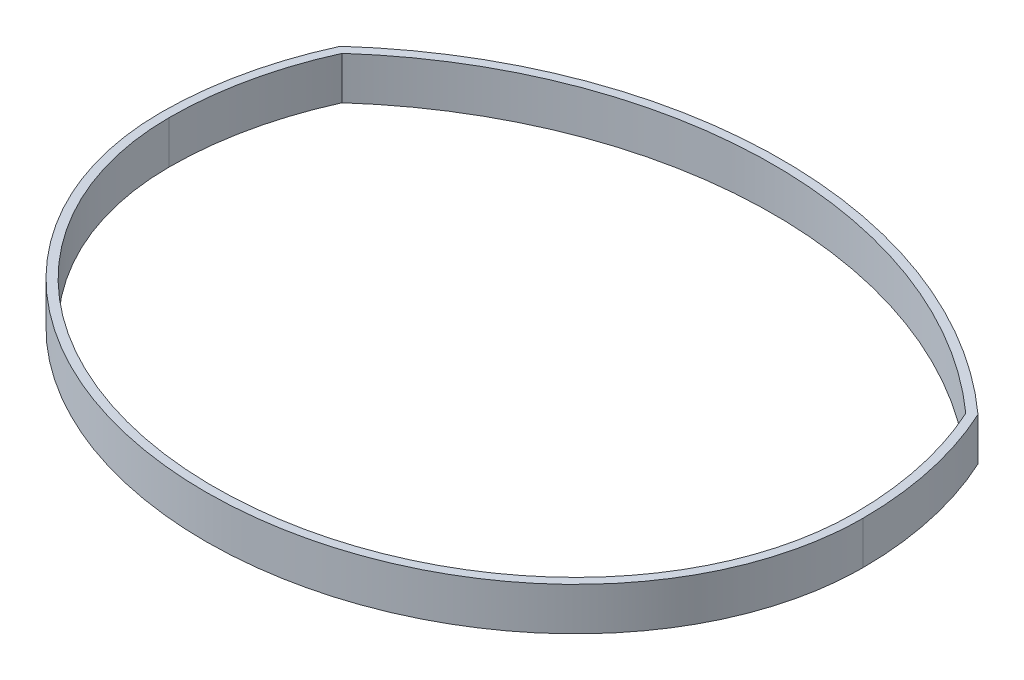
SolidWorks part; units mm, degrees
ref_plane "Front Plane" through (0, 0, 0) normal (0, 0, 1) x (1, 0, 0)
ref_plane "Top Plane" through (0, 0, 0) normal (0, 1, 0) x (1, 0, 0)
ref_plane "Right Plane" through (0, 0, 0) normal (1, 0, 0) x (0, 0, -1)
sketch "Sketch1" plane through (0, 0, 0) normal (0, 1, 0) x (1, 0, 0)
  line L0 (0, 118.5937) -> (0, 77.4941)
  arc A0 (-92.4508, 42.1356) -> (-101.6, 0) centre (0, 0) ccw
  arc A1 (92.4508, 42.1356) -> (-92.4508, 42.1356) centre (0, -61.0492) ccw
  arc A3 (101.6, 0) -> (92.4508, 42.1356) centre (0, 0) ccw
  arc A4 (94.5401, 43.6726) -> (-94.5401, 43.6726) centre (0, -61.0492) ccw
  arc A5 (-94.5401, 43.6726) -> (-104.14, 0) centre (0, 0) ccw
  arc A6 (104.14, 0) -> (94.5401, 43.6726) centre (0, 0) ccw
  ellipse E0 centre (0, 0) end of major axis (-101.6, 0) minor radius 88.1895 (-101.6, 0) -> (101.6, 0) ccw
  spline S0 degree 1 poles (-104.14, 0) (104.14, 0) knots 0 0 1 1 construction
  spline S1 degree 3 poles (-104.14, 0) (-104.14, -11.915) (-98.6678, -35.7775) (-75.4038, -65.9617) (-40.7591, -86.0412) (0, -93.0736) (40.7591, -86.0412) (75.4038, -65.9617) (98.6678, -35.7775) (104.14, -11.915) (104.14, 0) knots 0 0 0 0 0.392699 0.785398 1.178097 1.570796 1.963495 2.356194 2.748894 3.141593 3.141593 3.141593 3.141593
  point P10 (0, -88.1895)
  dimension "D2" = 2.54
  dimension "D1" = 203.2
extrude "Boss-Extrude1" add sketch "Sketch1" along normal blind 12.7
